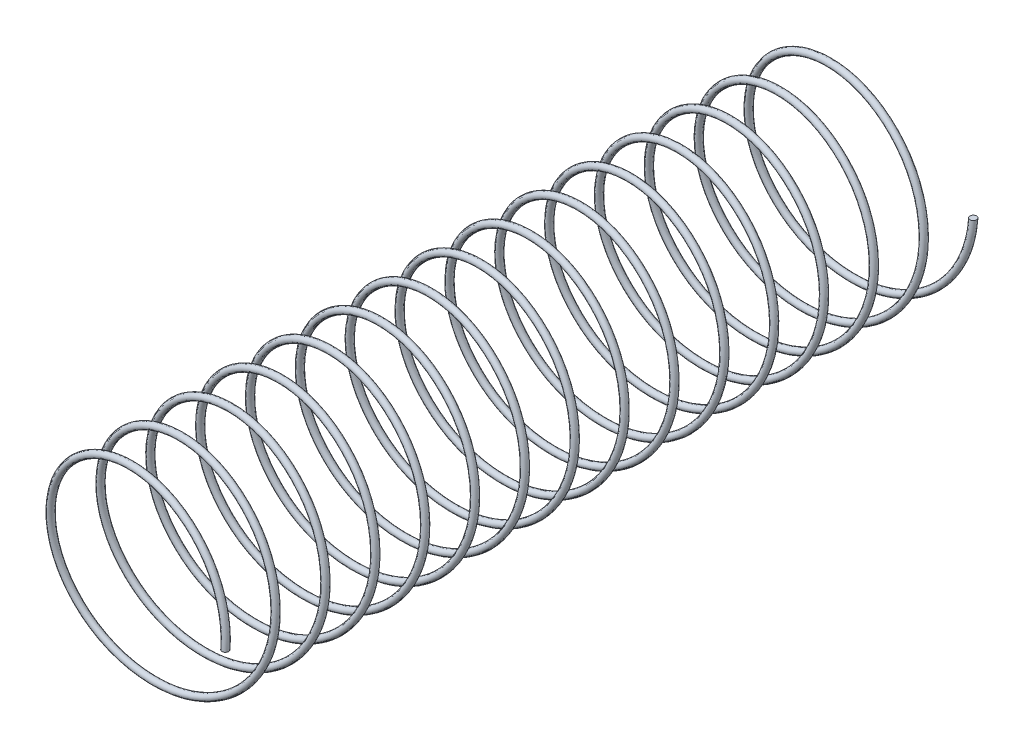
SolidWorks part; units mm, degrees
ref_plane "前视基准面" through (0, 0, 0) normal (0, 0, 1) x (1, 0, 0)
ref_plane "上视基准面" through (0, 0, 0) normal (0, 1, 0) x (1, 0, 0)
ref_plane "右视基准面" through (0, 0, 0) normal (1, 0, 0) x (0, 0, -1)
sketch "草图1" plane through (0, 0, 0) normal (0, 0, 1) x (1, 0, 0)
  circle A1 centre (0, 0) radius 3
  dimension "D1" = 6
curve "螺旋线/涡状线1" pitch 1.5 height 22.5 turns 15
sketch "草图2" plane through (0, 0, 0) normal (0, 1, 0) x (1, 0, 0)
  circle A0 centre (3, -22.5) radius 0.1
  spline S0 degree 3 poles (3, 0) (3, -0.0311) (2.8438, -0.0938) (2.1765, -0.1875) (1.1779, -0.2813) (0, -0.375) (-1.1779, -0.4688) (-2.1765, -0.5625) (-2.8438, -0.6563) (-3.0781, -0.75) (-2.8438, -0.8438) (-2.1765, -0.9375) (-1.1779, -1.0313) (0, -1.125) (1.1779, -1.2188) (2.1765, -1.3125) (2.8438, -1.4063) (3.0781, -1.5) (2.8438, -1.5938) (2.1765, -1.6875) (1.1779, -1.7813) (0, -1.875) (-1.1779, -1.9688) (-2.1765, -2.0625) (-2.8438, -2.1563) (-3.0781, -2.25) (-2.8438, -2.3438) (-2.1765, -2.4375) (-1.1779, -2.5313) (0, -2.625) (1.1779, -2.7188) (2.1765, -2.8125) (2.8438, -2.9063) (3.0781, -3) (2.8438, -3.0938) (2.1765, -3.1875) (1.1779, -3.2813) (0, -3.375) (-1.1779, -3.4688) (-2.1765, -3.5625) (-2.8438, -3.6563) (-3.0781, -3.75) (-2.8438, -3.8438) (-2.1765, -3.9375) (-1.1779, -4.0313) (0, -4.125) (1.1779, -4.2188) (2.1765, -4.3125) (2.8438, -4.4063) (3.0781, -4.5) (2.8438, -4.5938) (2.1765, -4.6875) (1.1779, -4.7813) (0, -4.875) (-1.1779, -4.9688) (-2.1765, -5.0625) (-2.8438, -5.1563) (-3.0781, -5.25) (-2.8438, -5.3438) (-2.1765, -5.4375) (-1.1779, -5.5313) (0, -5.625) (1.1779, -5.7188) (2.1765, -5.8125) (2.8438, -5.9063) (3.0781, -6) (2.8438, -6.0938) (2.1765, -6.1875) (1.1779, -6.2813) (0, -6.375) (-1.1779, -6.4688) (-2.1765, -6.5625) (-2.8438, -6.6563) (-3.0781, -6.75) (-2.8438, -6.8438) (-2.1765, -6.9375) (-1.1779, -7.0313) (0, -7.125) (1.1779, -7.2188) (2.1765, -7.3125) (2.8438, -7.4063) (3.0781, -7.5) (2.8438, -7.5938) (2.1765, -7.6875) (1.1779, -7.7813) (0, -7.875) (-1.1779, -7.9688) (-2.1765, -8.0625) (-2.8438, -8.1563) (-3.0781, -8.25) (-2.8438, -8.3438) (-2.1765, -8.4375) (-1.1779, -8.5313) (0, -8.625) (1.1779, -8.7188) (2.1765, -8.8125) (2.8438, -8.9063) (3.0781, -9) (2.8438, -9.0938) (2.1765, -9.1875) (1.1779, -9.2813) (0, -9.375) (-1.1779, -9.4688) (-2.1765, -9.5625) (-2.8438, -9.6563) (-3.0781, -9.75) (-2.8438, -9.8438) (-2.1765, -9.9375) (-1.1779, -10.0313) (0, -10.125) (1.1779, -10.2188) (2.1765, -10.3125) (2.8438, -10.4063) (3.0781, -10.5) (2.8438, -10.5938) (2.1765, -10.6875) (1.1779, -10.7813) (0, -10.875) (-1.1779, -10.9688) (-2.1765, -11.0625) (-2.8438, -11.1563) (-3.0781, -11.25) (-2.8438, -11.3438) (-2.1765, -11.4375) (-1.1779, -11.5313) (0, -11.625) (1.1779, -11.7188) (2.1765, -11.8125) (2.8438, -11.9063) (3.0781, -12) (2.8438, -12.0938) (2.1765, -12.1875) (1.1779, -12.2813) (0, -12.375) (-1.1779, -12.4688) (-2.1765, -12.5625) (-2.8438, -12.6563) (-3.0781, -12.75) (-2.8438, -12.8438) (-2.1765, -12.9375) (-1.1779, -13.0313) (0, -13.125) (1.1779, -13.2188) (2.1765, -13.3125) (2.8438, -13.4063) (3.0781, -13.5) (2.8438, -13.5938) (2.1765, -13.6875) (1.1779, -13.7813) (0, -13.875) (-1.1779, -13.9688) (-2.1765, -14.0625) (-2.8438, -14.1563) (-3.0781, -14.25) (-2.8438, -14.3438) (-2.1765, -14.4375) (-1.1779, -14.5313) (0, -14.625) (1.1779, -14.7188) (2.1765, -14.8125) (2.8438, -14.9063) (3.0781, -15) (2.8438, -15.0938) (2.1765, -15.1875) (1.1779, -15.2813) (0, -15.375) (-1.1779, -15.4688) (-2.1765, -15.5625) (-2.8438, -15.6563) (-3.0781, -15.75) (-2.8438, -15.8438) (-2.1765, -15.9375) (-1.1779, -16.0313) (0, -16.125) (1.1779, -16.2188) (2.1765, -16.3125) (2.8438, -16.4063) (3.0781, -16.5) (2.8438, -16.5938) (2.1765, -16.6875) (1.1779, -16.7813) (0, -16.875) (-1.1779, -16.9688) (-2.1765, -17.0625) (-2.8438, -17.1563) (-3.0781, -17.25) (-2.8438, -17.3438) (-2.1765, -17.4375) (-1.1779, -17.5313) (0, -17.625) (1.1779, -17.7188) (2.1765, -17.8125) (2.8438, -17.9063) (3.0781, -18) (2.8438, -18.0938) (2.1765, -18.1875) (1.1779, -18.2813) (0, -18.375) (-1.1779, -18.4688) (-2.1765, -18.5625) (-2.8438, -18.6563) (-3.0781, -18.75) (-2.8438, -18.8438) (-2.1765, -18.9375) (-1.1779, -19.0313) (0, -19.125) (1.1779, -19.2188) (2.1765, -19.3125) (2.8438, -19.4063) (3.0781, -19.5) (2.8438, -19.5938) (2.1765, -19.6875) (1.1779, -19.7813) (0, -19.875) (-1.1779, -19.9688) (-2.1765, -20.0625) (-2.8438, -20.1563) (-3.0781, -20.25) (-2.8438, -20.3438) (-2.1765, -20.4375) (-1.1779, -20.5313) (0, -20.625) (1.1779, -20.7188) (2.1765, -20.8125) (2.8438, -20.9062) (3.0781, -21) (2.8438, -21.0937) (2.1765, -21.1875) (1.1779, -21.2812) (0, -21.375) (-1.1779, -21.4687) (-2.1765, -21.5625) (-2.8438, -21.6562) (-3.0781, -21.75) (-2.8438, -21.8437) (-2.1765, -21.9375) (-1.1779, -22.0312) (0, -22.125) (1.1779, -22.2187) (2.1765, -22.3125) (2.8438, -22.4062) (3, -22.4689) (3, -22.5) knots 0 0 0 0 0.004167 0.008333 0.0125 0.016667 0.020833 0.025 0.029167 0.033333 0.0375 0.041667 0.045833 0.05 0.054167 0.058333 0.0625 0.066667 0.070833 0.075 0.079167 0.083333 0.0875 0.091667 0.095833 0.1 0.104167 0.108333 0.1125 0.116667 0.120833 0.125 0.129167 0.133333 0.1375 0.141667 0.145833 0.15 0.154167 0.158333 0.1625 0.166667 0.170833 0.175 0.179167 0.183333 0.1875 0.191667 0.195833 0.2 0.204167 0.208333 0.2125 0.216667 0.220833 0.225 0.229167 0.233333 0.2375 0.241667 0.245833 0.25 0.254167 0.258333 0.2625 0.266667 0.270833 0.275 0.279167 0.283333 0.2875 0.291667 0.295833 0.3 0.304167 0.308333 0.3125 0.316667 0.320833 0.325 0.329167 0.333333 0.3375 0.341667 0.345833 0.35 0.354167 0.358333 0.3625 0.366667 0.370833 0.375 0.379167 0.383333 0.3875 0.391667 0.395833 0.4 0.404167 0.408333 0.4125 0.416667 0.420833 0.425 0.429167 0.433333 0.4375 0.441667 0.445833 0.45 0.454167 0.458333 0.4625 0.466667 0.470833 0.475 0.479167 0.483333 0.4875 0.491667 0.495833 0.5 0.504167 0.508333 0.5125 0.516667 0.520833 0.525 0.529167 0.533333 0.5375 0.541667 0.545833 0.55 0.554167 0.558333 0.5625 0.566667 0.570833 0.575 0.579167 0.583333 0.5875 0.591667 0.595833 0.6 0.604167 0.608333 0.6125 0.616667 0.620833 0.625 0.629167 0.633333 0.6375 0.641667 0.645833 0.65 0.654167 0.658333 0.6625 0.666667 0.670833 0.675 0.679167 0.683333 0.6875 0.691667 0.695833 0.7 0.704167 0.708333 0.7125 0.716667 0.720833 0.725 0.729167 0.733333 0.7375 0.741667 0.745833 0.75 0.754167 0.758333 0.7625 0.766667 0.770833 0.775 0.779167 0.783333 0.7875 0.791667 0.795833 0.8 0.804167 0.808333 0.8125 0.816667 0.820833 0.825 0.829167 0.833333 0.8375 0.841667 0.845833 0.85 0.854167 0.858333 0.8625 0.866667 0.870833 0.875 0.879167 0.883333 0.8875 0.891667 0.895833 0.9 0.904167 0.908333 0.9125 0.916667 0.920833 0.925 0.929167 0.933333 0.9375 0.941667 0.945833 0.95 0.954167 0.958333 0.9625 0.966667 0.970833 0.975 0.979167 0.983333 0.9875 0.991667 0.995833 1 1 1 1 construction
  dimension "D1" = 0.2
sweep "扫描1" add profiles "草图2" path "螺旋线/涡状线1"
